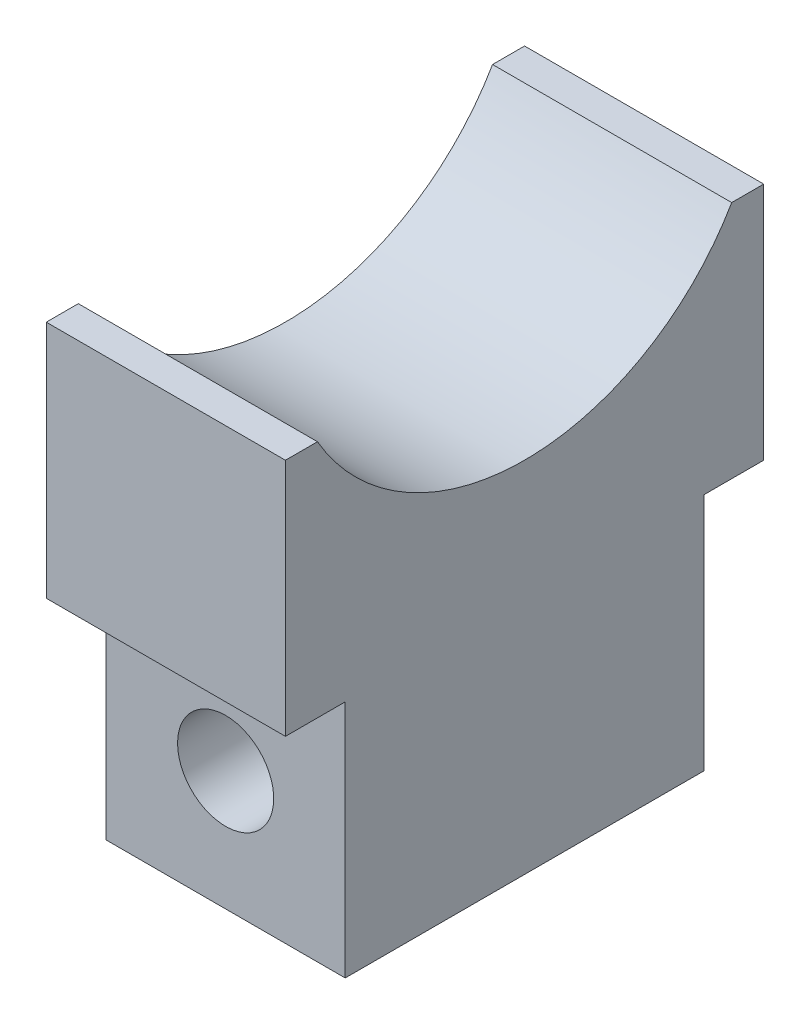
SolidWorks part; units mm, degrees
ref_plane "Front" through (0, 0, 0) normal (0, 0, 1) x (1, 0, 0)
ref_plane "Top" through (0, 0, 0) normal (0, 1, 0) x (1, 0, 0)
ref_plane "Right" through (0, 0, 0) normal (1, 0, 0) x (0, 0, -1)
sketch "Sketch1" plane through (0, 0, 0) normal (0, 0, 1) x (1, 0, 0)
  line L1 (6.35, -12.7) -> (-6.35, -12.7)
  line L2 (6.35, -12.7) -> (6.35, 12.7)
  line L3 (6.35, 12.7) -> (-6.35, 12.7)
  line L4 (-6.35, -12.7) -> (-6.35, 12.7)
  line L5 (6.35, -12.7) -> (-6.35, 12.7) construction
  line L6 (6.35, 12.7) -> (-6.35, -12.7) construction
  point P0 (0, 0)
  dimension "D1" = 25.4
  dimension "D2" = 12.7
extrude "Boss-Extrude1" add sketch "Sketch1" along normal blind 25.4
sketch "Sketch2" plane through (-6.35, 0, 0) normal (-1, 0, 0) x (0, 0, 1)
  line L14 (25.4, 12.7) -> (0, 12.7) construction
  line L15 (23.6985, 12.7) -> (25.4, 12.7)
  line L16 (25.4, 12.7) -> (25.4, 0)
  line L18 (25.4, 0) -> (22.225, 0)
  line L19 (22.225, 0) -> (22.225, -12.7)
  line L20 (25.4, -12.7) -> (0, -12.7) construction
  line L21 (22.225, -12.7) -> (3.175, -12.7)
  line L22 (3.175, -12.7) -> (3.175, 0)
  line L23 (3.175, 0) -> (0, 0)
  line L24 (0, 12.7) -> (0, -12.7) construction
  line L25 (0, 0) -> (0, 12.7)
  line L26 (0, 12.7) -> (1.7015, 12.7)
  line L27 (25.4, 12.7) -> (25.4, -12.7) construction
  arc A2 (1.7015, 12.7) -> (23.6985, 12.7) centre (12.7, 19.05) ccw
  point P3 (12.7, 12.7)
  dimension "D1" = 3.175
  dimension "D3" = 12.7
  dimension "D2" = 3.175
  dimension "D4" = 6.35
extrude "Cut-Extrude1" cut sketch "Sketch2" against normal through all flip side to cut
hole_wizard "1/4-20 Tapped Hole2" positions "3DSketch2" profile "Sketch5" tap size "1/4-20" standard "ANSI Inch" end condition through all
sketch3d "3DSketch2"
  line L1 (0, 0, 3.175) -> (0, -12.7, 3.175) construction
  line L4 (6.35, 0, 3.175) -> (-6.35, 0, 3.175) construction
  line L5 (6.35, -12.7, 3.175) -> (-6.35, -12.7, 3.175) construction
  point P12 (0, -6.35, 3.175)
sketch "Sketch5" plane through (0, -6.35, 3.175) normal (1, 0, 0) x (0, 1, 0)
  line L0 (0, 0) -> (0, 22.225)
  line L1 (0, 22.225) -> (2.5527, 22.225)
  line L2 (2.5527, 22.225) -> (2.5527, 0)
  line L5 (2.5527, 0) -> (0, 0)
  line L11 (0, -6.35) -> (0, 107.95) construction
  dimension "Thru Tap Drill Dia." = 5.1054
  dimension "Thru Tap Drill Depth" = 22.225
cosmetic thread "Hole Thread1" parameters "D2"=6.35
